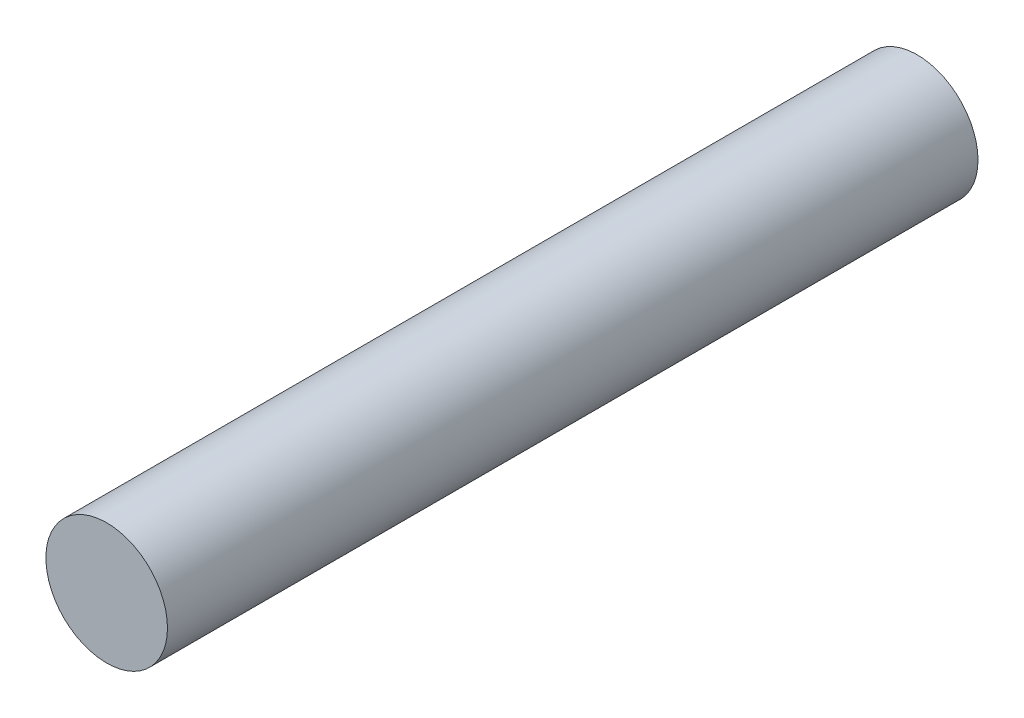
SolidWorks part; units mm, degrees
ref_plane "Face" through (0, 0, 0) normal (0, 0, 1) x (1, 0, 0)
ref_plane "Dessus" through (0, 0, 0) normal (0, 1, 0) x (1, 0, 0)
ref_plane "Droite" through (0, 0, 0) normal (1, 0, 0) x (0, 0, -1)
sketch "Esquisse1" plane through (0, 0, 0) normal (0, 0, 1) x (1, 0, 0)
  circle A3 centre (0, 0) radius 3
  dimension "D1" = 6
extrude "Boss.-Extru.1" add sketch "Esquisse1" along normal mid plane 40
